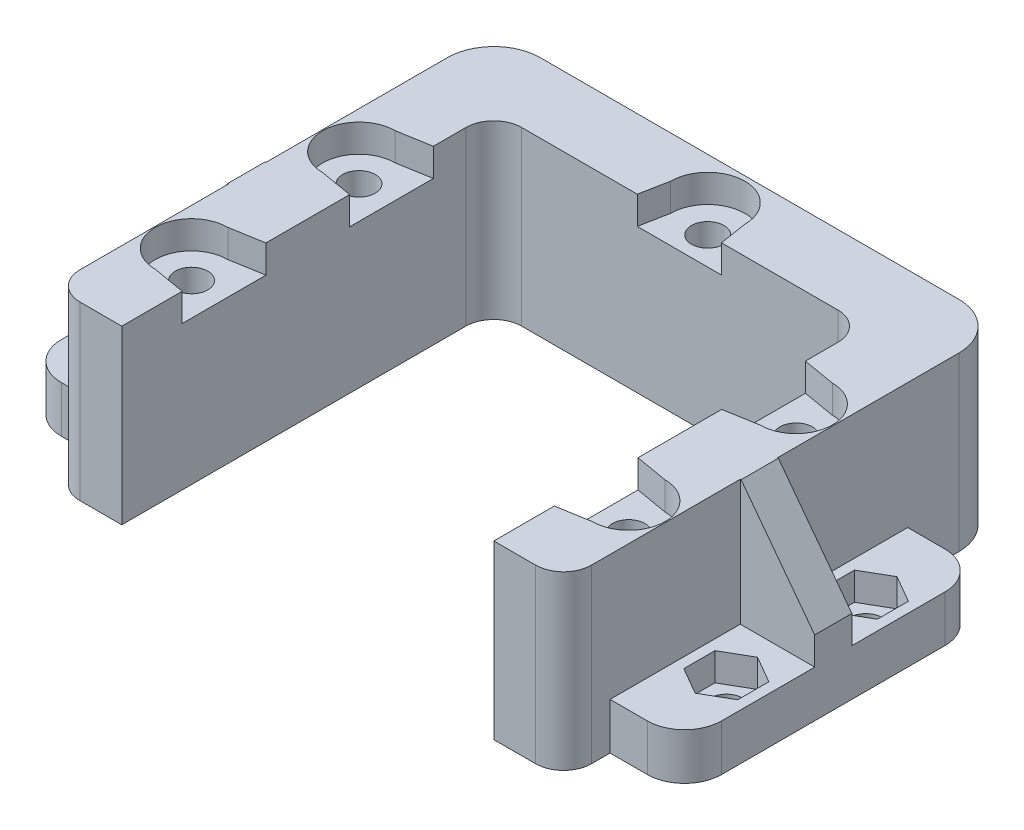
SolidWorks part; units mm, degrees
ref_plane "Front Plane" through (0, 0, 0) normal (0, 0, 1) x (1, 0, 0)
ref_plane "Top Plane" through (0, 0, 0) normal (0, 1, 0) x (1, 0, 0)
ref_plane "Right Plane" through (0, 0, 0) normal (1, 0, 0) x (0, 0, -1)
sketch "Sketch1" plane through (0, 0, 0) normal (0, 1, 0) x (1, 0, 0)
  line L0 (-20, -20) -> (-24.5, -20)
  line L1 (-17, 20) -> (17, 20)
  line L2 (-20, 17) -> (-20, -20)
  line L4 (20, 17) -> (20, -20)
  line L5 (-20, 20) -> (20, -20) construction
  line L6 (-20, -20) -> (20, 20) construction
  line L7 (-22.5, 27.5) -> (22.5, 27.5)
  line L8 (-27.5, 22.5) -> (-27.5, -17)
  line L10 (27.5, 22.5) -> (27.5, -17)
  line L11 (-27.5, 27.5) -> (27.5, -27.5) construction
  line L12 (-27.5, -27.5) -> (27.5, 27.5) construction
  line L13 (20, -20) -> (24.5, -20)
  arc A0 (17, 20) -> (20, 17) centre (17, 17) cw
  arc A1 (-17, 20) -> (-20, 17) centre (-17, 17) ccw
  arc A2 (22.5, 27.5) -> (27.5, 22.5) centre (22.5, 22.5) cw
  arc A3 (-22.5, 27.5) -> (-27.5, 22.5) centre (-22.5, 22.5) ccw
  arc A4 (24.5, -20) -> (27.5, -17) centre (24.5, -17) ccw
  arc A5 (-24.5, -20) -> (-27.5, -17) centre (-24.5, -17) cw
  point P0 (0, 0)
  point P12 (0, 0)
  dimension "D3" = 3
  dimension "D6" = 5
  dimension "D7" = 3
  dimension "D1" = 40
  dimension "D2" = 40
  dimension "D4" = 55
  dimension "D5" = 55
extrude "Boss-Extrude1" add sketch "Sketch1" along normal blind 18.5
sketch "Sketch2" plane through (0, 18.5, 0) normal (0, 1, 0) x (1, 0, 0)
  line L0 (-23.5, -9) -> (23.5, -9) construction
  line L1 (0, -9) -> (0, -20) construction
  line L4 (-20, -20) -> (20, -20) construction
  line L5 (0, 20) -> (0, 23) construction
  line L6 (-17, 20) -> (17, 20) construction
  line L7 (-23.5, 9) -> (23.5, 9) construction
  line L8 (0, 9) -> (0, 20) construction
  circle A0 centre (-23.5, -9) radius 1.75
  circle A1 centre (23.5, -9) radius 1.75
  circle A2 centre (0, 23) radius 1.75
  circle A3 centre (-23.5, 9) radius 1.75
  circle A4 centre (23.5, 9) radius 1.75
  dimension "D3" = 3.5
  dimension "D4" = 3.5
  dimension "D6" = 3.5
  dimension "D9" = 3.5
  dimension "D10" = 3.5
  dimension "D1" = 11
  dimension "D2" = 47
  dimension "D5" = 3
  dimension "47" = 47
  dimension "D8" = 11
extrude "Cut-Extrude1" cut sketch "Sketch2" against normal blind 15.5
sketch "Sketch3" plane through (0, 0, 0) normal (0, -1, 0) x (1, 0, 0)
  line L1 (-20.6, 7.3257) -> (-20.6, 10.6743)
  line L2 (-20.6, 10.6743) -> (-23.5, 12.3486)
  line L3 (-23.5, 12.3486) -> (-26.4, 10.6743)
  line L4 (-26.4, 10.6743) -> (-26.4, 7.3257)
  line L5 (-26.4, 7.3257) -> (-23.5, 5.6514)
  line L6 (-23.5, 5.6514) -> (-20.6, 7.3257)
  line L7 (23.4997, 5.6514) -> (26.3998, 7.3254)
  line L8 (26.3998, 7.3254) -> (26.4002, 10.674)
  line L9 (26.4002, 10.674) -> (23.5003, 12.3486)
  line L10 (23.5003, 12.3486) -> (20.6002, 10.6746)
  line L11 (20.6002, 10.6746) -> (20.5998, 7.326)
  line L12 (20.5998, 7.326) -> (23.4997, 5.6514)
  line L13 (3.3486, -23) -> (1.6743, -20.1)
  line L14 (1.6743, -20.1) -> (-1.6743, -20.1)
  line L15 (-1.6743, -20.1) -> (-3.3486, -23)
  line L16 (-3.3486, -23) -> (-1.6743, -25.9)
  line L17 (-1.6743, -25.9) -> (1.6743, -25.9)
  line L18 (1.6743, -25.9) -> (3.3486, -23)
  line L19 (-23.4997, -5.6514) -> (-26.3998, -7.3254)
  line L20 (-26.3998, -7.3254) -> (-26.4002, -10.674)
  line L21 (-26.4002, -10.674) -> (-23.5003, -12.3486)
  line L22 (-23.5003, -12.3486) -> (-20.6002, -10.6746)
  line L23 (-20.6002, -10.6746) -> (-20.5998, -7.326)
  line L24 (-20.5998, -7.326) -> (-23.4997, -5.6514)
  line L25 (23.4997, -5.6514) -> (20.5998, -7.326)
  line L26 (20.5998, -7.326) -> (20.6002, -10.6746)
  line L27 (20.6002, -10.6746) -> (23.5003, -12.3486)
  line L28 (23.5003, -12.3486) -> (26.4002, -10.674)
  line L29 (26.4002, -10.674) -> (26.3998, -7.3254)
  line L30 (26.3998, -7.3254) -> (23.4997, -5.6514)
  circle A0 centre (-23.5, 9) radius 2.9 construction
  circle A1 centre (23.5, 9) radius 2.9 construction
  circle A2 centre (0, -23) radius 2.9 construction
  circle A3 centre (-23.5, -9) radius 2.9 construction
  circle A4 centre (23.5, -9) radius 2.9 construction
  dimension "D1" = 5.8
  dimension "D2" = 5.8
  dimension "D3" = 5.8
  dimension "D4" = 5.8
  dimension "D5" = 5.8
extrude "Cut-Extrude2" cut sketch "Sketch3" against normal blind 3
sketch "Sketch4" plane through (-27.5, 0, 0) normal (-1, 0, 0) x (0, 0, 1)
  line L0 (-22.5, 0) -> (17, 0) construction
  line L1 (-17, 0) -> (15, 0)
  line L2 (-17, 0) -> (-17, 5)
  line L3 (-17, 5) -> (15, 5)
  line L4 (15, 0) -> (15, 5)
  line L5 (20, 18.5) -> (20, 0) construction
  dimension "D1" = 5
  dimension "D2" = 32
  dimension "D3" = 5
extrude "Boss-Extrude2" add sketch "Sketch4" along normal blind 8
fillet "Fillet1" radius 4 2 edges at (-35.5, 2.5, 15) (-35.5, 2.5, -17)
sketch "Sketch5" plane through (0, 5, 0) normal (0, 1, 0) x (1, 0, 0)
  line L0 (-35.5, 8.5) -> (-27.5, 8.5) construction
  line L1 (-35.5, -11) -> (-35.5, 13) construction
  line L2 (-27.5, 22.5) -> (-27.5, -17) construction
  line L3 (-31.5, 8.5) -> (-31.5, -6.5) construction
  line L4 (-31.5, 1) -> (-35.5, 1) construction
  circle A0 centre (-31.5, 8.5) radius 1.75
  circle A1 centre (-31.5, -6.5) radius 1.75
  dimension "D1" = 3.5
  dimension "D2" = 3.5
  dimension "D3" = 15
extrude "Cut-Extrude3" cut sketch "Sketch5" against normal blind 6
sketch "Sketch6" plane through (-27.5, 0, 0) normal (-1, 0, 0) x (0, 0, 1)
  line L0 (11, 5) -> (-13, 5) construction
  line L1 (-3, 5) -> (1, 5)
  line L2 (-3, 5) -> (-3, 18.5)
  line L3 (-3, 18.5) -> (1, 18.5)
  line L4 (1, 5) -> (1, 18.5)
  line L5 (-22.5, 18.5) -> (17, 18.5) construction
  dimension "D1" = 4
  dimension "D2" = 14
  dimension "D3" = 14
extrude "Boss-Extrude3" add sketch "Sketch6" along normal blind 8
chamfer "Chamfer1" distance 10.5 angle 37 1 edges at (-35.5, 18.5, -1)
sketch "Sketch7" plane through (0, 5, 0) normal (0, 1, 0) x (1, 0, 0)
  line L1 (-31.5, 11.8486) -> (-34.4, 10.1743)
  line L2 (-34.4, 10.1743) -> (-34.4, 6.8257)
  line L3 (-34.4, 6.8257) -> (-31.5, 5.1514)
  line L4 (-31.5, 5.1514) -> (-28.6, 6.8257)
  line L5 (-28.6, 6.8257) -> (-28.6, 10.1743)
  line L6 (-28.6, 10.1743) -> (-31.5, 11.8486)
  line L7 (-31.5, -3.1514) -> (-34.4, -4.8257)
  line L8 (-34.4, -4.8257) -> (-34.4, -8.1743)
  line L9 (-34.4, -8.1743) -> (-31.5, -9.8486)
  line L10 (-31.5, -9.8486) -> (-28.6, -8.1743)
  line L11 (-28.6, -8.1743) -> (-28.6, -4.8257)
  line L12 (-28.6, -4.8257) -> (-31.5, -3.1514)
  circle A0 centre (-31.5, 8.5) radius 2.9 construction
  circle A1 centre (-31.5, -6.5) radius 2.9 construction
  dimension "D1" = 5.8
  dimension "D2" = 5.8
extrude "Cut-Extrude4" cut sketch "Sketch7" against normal blind 3
mirror "Mirror1" about plane through (0, 0, 0) normal (1, 0, 0) of "Cut-Extrude4", "Chamfer1", "Boss-Extrude3", "Cut-Extrude3", "Fillet1", "Boss-Extrude2"
sketch "Sketch8" plane through (0, 18.5, 0) normal (0, 1, 0) x (1, 0, 0)
  line L0 (-4, 23) -> (-4.5746, 20)
  line L1 (-17, 20) -> (17, 20) construction
  line L2 (-4.5746, 20) -> (4.4783, 20)
  line L3 (4.4783, 20) -> (4, 23)
  line L4 (23.5, 12.9) -> (20, 13.5)
  line L5 (20, 17) -> (20, -20) construction
  line L6 (20, 13.5) -> (20, 4.5)
  line L7 (20, 4.5) -> (23.5, 5.1)
  line L8 (23.5, -5.1) -> (20, -4.5)
  line L9 (20, -4.5) -> (20, -13.5)
  line L10 (20, -13.5) -> (23.5, -12.9)
  line L11 (-23.5, -12.9) -> (-20, -13.5)
  line L12 (-20, -20) -> (-20, 17) construction
  line L13 (-20, -13.5) -> (-20, -4.5)
  line L14 (-20, -4.5) -> (-23.5, -5.1)
  line L15 (-20, -9) -> (-23.5, -9) construction
  line L16 (20, -9) -> (23.5, -9) construction
  line L17 (20, 9) -> (23.5, 9) construction
  line L18 (-0.0481, 20) -> (0, 23) construction
  line L19 (-23.5, 12.9) -> (-20, 13.5)
  line L20 (-20, 13.5) -> (-20, 4.5)
  line L21 (-20, 4.5) -> (-23.5, 5.1)
  line L22 (-23.5, 9) -> (-20, 9) construction
  arc A0 (4, 23) -> (-4, 23) centre (0, 23) ccw
  arc A1 (-23.5, 12.9) -> (-23.5, 5.1) centre (-23.5, 9) ccw
  arc A2 (-23.5, -5.1) -> (-23.5, -12.9) centre (-23.5, -9) ccw
  arc A4 (23.5, -12.9) -> (23.5, -5.1) centre (23.5, -9) ccw
  arc A5 (23.5, 5.1) -> (23.5, 12.9) centre (23.5, 9) ccw
  dimension "D1" = 9
  dimension "D2" = 9
  dimension "D3" = 9
  dimension "D4" = 9
extrude "Cut-Extrude7" cut sketch "Sketch8" against normal blind 3
